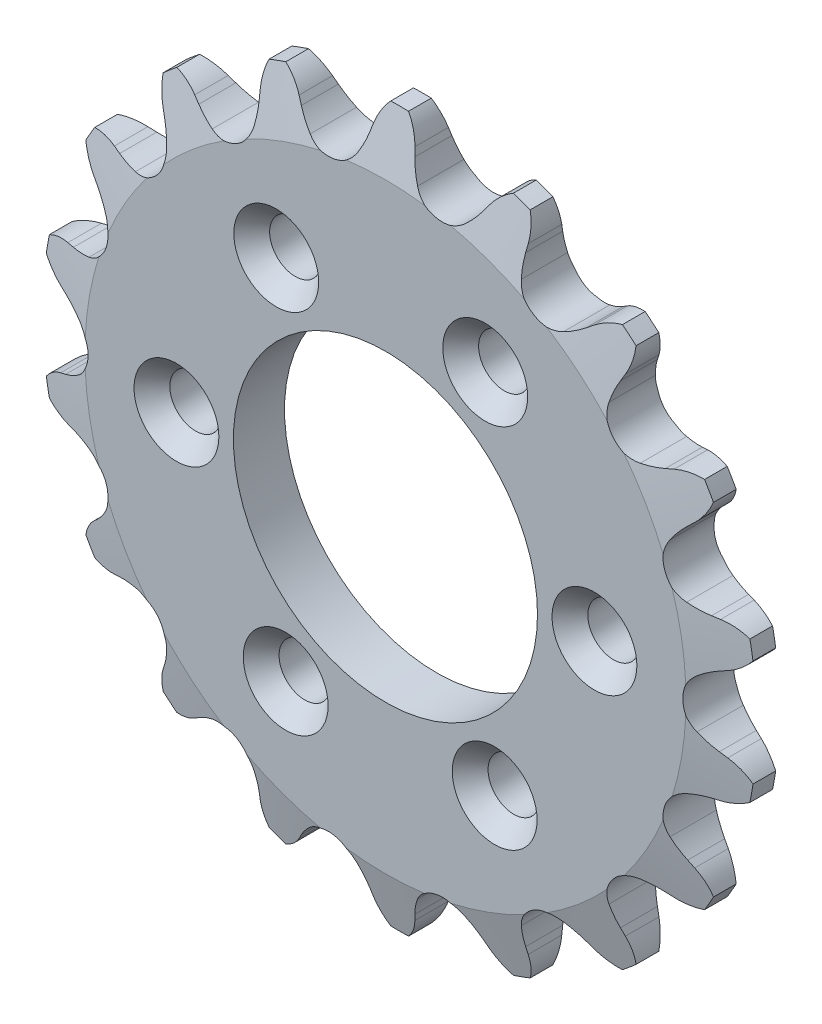
SolidWorks part; units mm, degrees
ref_plane "Front Plane" through (0, 0, 0) normal (0, 0, 1) x (1, 0, 0)
ref_plane "Top Plane" through (0, 0, 0) normal (0, 1, 0) x (1, 0, 0)
ref_plane "Right Plane" through (0, 0, 0) normal (1, 0, 0) x (0, 0, -1)
sketch "Sketch0" plane through (0, 0, 0) normal (0, 0, 1) x (1, 0, 0)
  line L0 (4.7625, -27.0095) -> (0, 0) construction
  line L1 (0, 0) -> (13.7131, -23.7517) construction
  line L2 (0, 0) -> (-4.7625, -27.0095) construction
  line L3 (4.7625, -27.0095) -> (13.7131, -23.7517) construction
  line L4 (4.7625, -27.0095) -> (-4.7625, -27.0095) construction
  line L5 (7.9495, -26.8862) -> (7.6137, -26.3777)
  line L6 (4.7625, -27.0095) -> (0, -27.8492) construction
  line L7 (1.7255, -27.9836) -> (1.8672, -27.391)
  line L8 (0, -27.0095) -> (0, -29.867) construction
  line L9 (6.4849, -25.0741) -> (2.0608, -30.0454) construction
  line L10 (0, 0) -> (0, -27.0095) construction
  line L11 (7.6137, -26.3777) -> (2.0608, -30.0454) construction
  line L12 (0, -29.867) -> (0, -30.4786) construction
  line L13 (11.4456, -24.577) -> (7.9495, -26.8862) construction
  circle A0 centre (0, 0) radius 29.867 construction
  circle A1 centre (0, 0) radius 27.4261 construction
  arc A2 (-2.7126, -31.1836) -> (13.2144, -28.3752) centre (0, 0) ccw
  circle A3 centre (0, 0) radius 30.4786 construction
  circle A4 centre (4.7625, -27.0095) radius 2.54 construction
  arc A7 (6.4849, -25.0741) -> (2.4821, -25.7799) centre (4.7625, -27.0095) ccw
  circle A8 centre (4.7625, -27.0095) radius 2.5908 construction
  arc A9 (7.9495, -26.8862) -> (13.2144, -28.3752) centre (11.4456, -24.577) ccw
  arc A10 (7.6137, -26.3777) -> (6.4849, -25.0741) centre (2.0608, -30.0454) ccw
  arc A11 (1.7255, -27.9836) -> (-2.7126, -31.1836) centre (-2.3495, -27.0095) cw
  arc A12 (1.8672, -27.391) -> (2.4821, -25.7799) centre (8.3396, -28.9383) cw
  dimension "D1" = 2.5908
  dimension "R" = 2.5908
sketch "Sketch1" plane through (0, 0, 0) normal (1, 0, 0) x (0, 0, -1)
  line L0 (2.1336, 0) -> (-2.1336, 0)
  line L1 (-2.1336, 0) -> (-2.1336, 25.1045)
  line L2 (-2.1336, 25.1045) -> (-0.943, 29.867)
  line L3 (-0.943, 29.867) -> (0.943, 29.867)
  line L4 (0.943, 29.867) -> (2.1336, 25.1045)
  line L5 (2.1336, 25.1045) -> (2.1336, 0)
  line L7 (0, 29.867) -> (0, 0) construction
  line L8 (-2.1336, 25.1045) -> (2.1336, 25.1045) construction
  line L9 (0, 29.867) -> (0, -29.867) construction
  line L10 (-2.1336, 25.1045) -> (-2.1336, 29.867) construction
  line L11 (-2.1336, 29.867) -> (-0.943, 29.867) construction
  line L12 (0.943, 29.867) -> (2.1336, 29.867) construction
  line L13 (2.1336, 29.867) -> (2.1336, 25.1045) construction
revolve "Revolve1" add sketch "Sketch1" angle 360 mid plane about L0
extrude "Cut-Extrude1" cut sketch "Sketch0" against normal through all and the other way through all
pattern_circular "CirPattern1" count 18 over 360 about axis through (0, 0, 0) along (0, 0, 1) of "Cut-Extrude1"
sketch "Sketch2" plane through (0, 0, 0) normal (0, 0, 1) x (1, 0, 0)
  circle A0 centre (0, 0) radius 6.35 construction
  circle A1 centre (0, 0) radius 30.1625
  circle A2 centre (0, 0) radius 29.845 construction
  dimension "Bore" = 12.7
  dimension "Hub Dia." = 60.325
  dimension "OD" = 59.69
sketch "Sketch3" plane through (0, 0, 0) normal (0, 0, 1) x (1, 0, 0)
  circle A0 centre (0, 0) radius 6.35 construction
  circle A1 centre (0, 0) radius 6.35
  circle A2 centre (0, 0) radius 29.845 construction
  circle A3 centre (0, 0) radius 29.845
extrude "Cut-Extrude2" cut sketch "Sketch3" along normal through all and the other way through all flip side to cut
sketch "Sketch4" plane through (0, 0, 2.1336) normal (0, 0, 1) x (1, 0, 0)
  circle A0 centre (0, 0) radius 12.7
  dimension "D1" = 25.4
extrude "Cut-Extrude3" cut sketch "Sketch4" against normal through all
sketch "Sketch5" plane through (0, 0, 2.1336) normal (0, 0, 1) x (1, 0, 0)
  line L0 (17.4566, 0.4556) -> (25.0959, 0.655)
  circle A0 centre (0, 0) radius 12.7
  circle A1 centre (0, 0) radius 25.1045
  circle A2 centre (0, 0) radius 17.4625
  point P8 (17.4566, 0.4556)
  dimension "D1" = 4.7625
hole_wizard "CSK for #6 Flat Head Machine Screw1" positions "Sketch8" profile "Sketch9" countersink size "#6" standard "ANSI Inch" end condition through all
sketch "Sketch8" plane through (0, 0, 2.1336) normal (0, 0, 1) x (1, 0, 0)
  point P0 (17.4566, 0.4556)
sketch "Sketch9" plane through (17.4566, 0.4556, 2.1336) normal (1, 0, 0) x (0, -1, 0)
  line L0 (0, 0) -> (0, 4.2672)
  line L1 (0, 4.2672) -> (2.1526, 4.2672)
  line L2 (2.1526, 4.2672) -> (2.1526, 1.5998)
  line L3 (2.1526, 1.5998) -> (3.5433, 0)
  line L5 (3.5433, 0) -> (0, 0)
  line L6 (-2.1526, 1.5998) -> (-3.5433, 0) construction
  line L11 (0, -6.35) -> (0, 107.95) construction
  dimension "Thru Hole Dia." = 4.3053
  dimension "Thru Hole Depth" = 4.2672
  dimension "Near C'Sink Dia." = 7.0866
  dimension "Near C'Sink Angle" = 82
pattern_circular "CirPattern2" count 6 over 360 about axis through (0, 0, 0) along (0, 0, 1) of "CSK for #6 Flat Head Machine Screw1"
equation "\"360/N@Sketch0\" = 360/\"Teeth@CirPattern1\""
equation "\"Ds@Sketch0\" = 1.005 * \"Dr@Sketch0\" + 0.003"
equation "\"R@Sketch0\" = 1/2 * \"Ds@Sketch0\""
equation "\"A@Sketch0\" = 35 +  ( 60 / \"Teeth@CirPattern1\" ) "
equation "\"B@Sketch0\" = 18 -  ( 56 / \"Teeth@CirPattern1\" )"
equation "\"ac@Sketch0\" = 0.8 * \"Dr@Sketch0\""
equation "\"ab@Sketch0\" = 1.4 * \"Dr@Sketch0\""
equation "\"J@Sketch0\" = 0.3 * \"Pitch@Sketch0\""
equation "\"h@Sketch1\" = \"Pitch@Sketch0\" / 2"
equation "\"g@Sketch1\" = \"h@Sketch1\" / 4"
